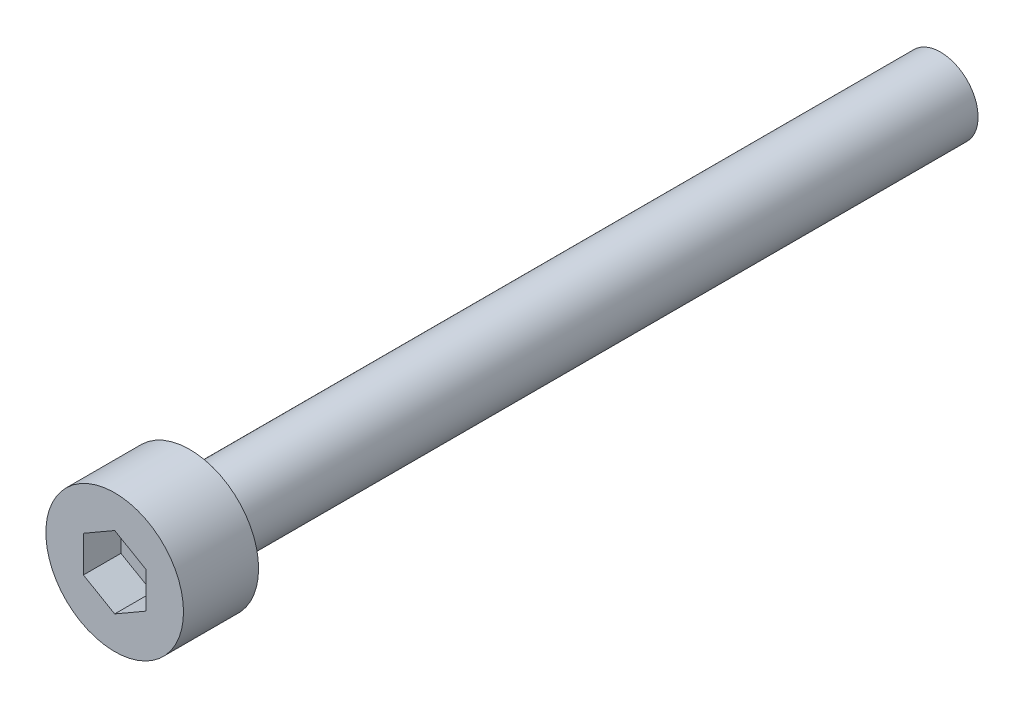
SolidWorks part; units mm, degrees
material "灰铸铁"
ref_plane "前视基准面" through (0, 0, 0) normal (0, 0, 1) x (1, 0, 0)
ref_plane "上视基准面" through (0, 0, 0) normal (0, 1, 0) x (1, 0, 0)
ref_plane "右视基准面" through (0, 0, 0) normal (1, 0, 0) x (0, 0, -1)
sketch "草图1" plane through (0, 0, 0) normal (0, 0, 1) x (1, 0, 0)
  circle A0 centre (0, 0) radius 2.75
  dimension "D1" = 5.5
extrude "凸台-拉伸1" add sketch "草图1" along normal blind 3
sketch "草图2" plane through (0, 0, 3) normal (0, 0, 1) x (1, 0, 0)
  line L1 (0, -1.4434) -> (1.25, -0.7217)
  line L2 (1.25, -0.7217) -> (1.25, 0.7217)
  line L3 (1.25, 0.7217) -> (0, 1.4434)
  line L4 (0, 1.4434) -> (-1.25, 0.7217)
  line L5 (-1.25, 0.7217) -> (-1.25, -0.7217)
  line L6 (-1.25, -0.7217) -> (0, -1.4434)
  circle A0 centre (0, 0) radius 1.25 construction
  dimension "D1" = 2.5
extrude "切除-拉伸1" cut sketch "草图2" against normal blind 1.5
sketch "草图3" plane through (0, 0, 0) normal (0, 0, -1) x (-1, 0, 0)
  circle A0 centre (0, 0) radius 1.5
extrude "凸台-拉伸2" add sketch "草图3" along normal blind 30
